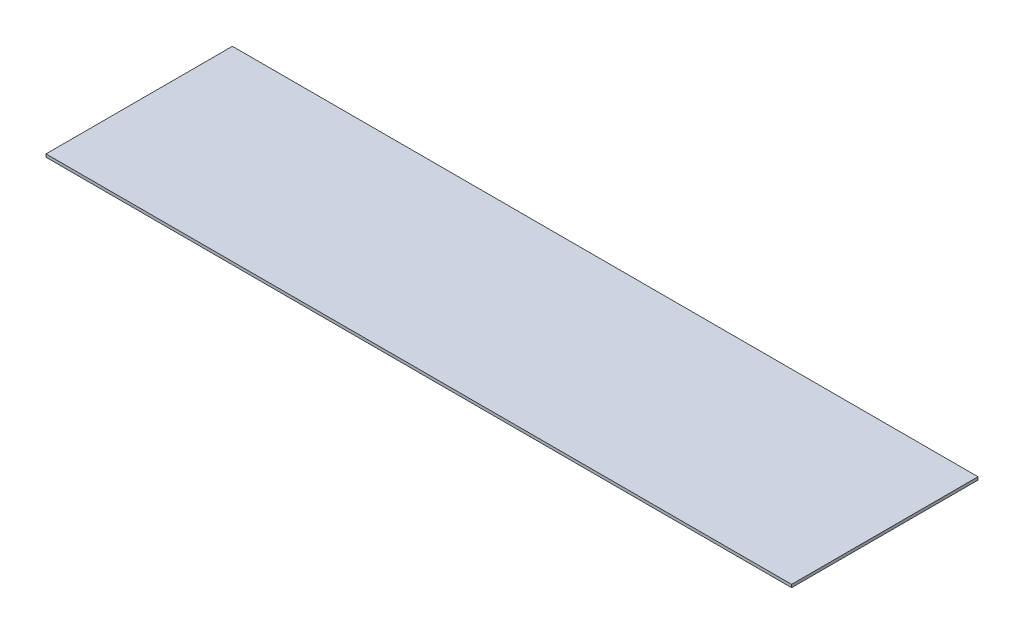
SolidWorks part; units mm, degrees
material "Nylon 101"
ref_plane "Front Plane" through (0, 0, 0) normal (0, 0, 1) x (1, 0, 0)
ref_plane "Top Plane" through (0, 0, 0) normal (0, 1, 0) x (1, 0, 0)
ref_plane "Right Plane" through (0, 0, 0) normal (1, 0, 0) x (0, 0, -1)
sketch "Sketch1" plane through (0, 0, 0) normal (0, -1, 0) x (1, 0, 0)
  line L2 (0, 0) -> (406.4, 0)
  line L3 (0, 0) -> (0, 101.6)
  line L4 (0, 101.6) -> (406.4, 101.6)
  line L5 (406.4, 0) -> (406.4, 101.6)
  dimension "D2" = 406.4
  dimension "D1" = 101.6
extrude "Boss-Extrude1" add sketch "Sketch1" along normal blind 1.5875
